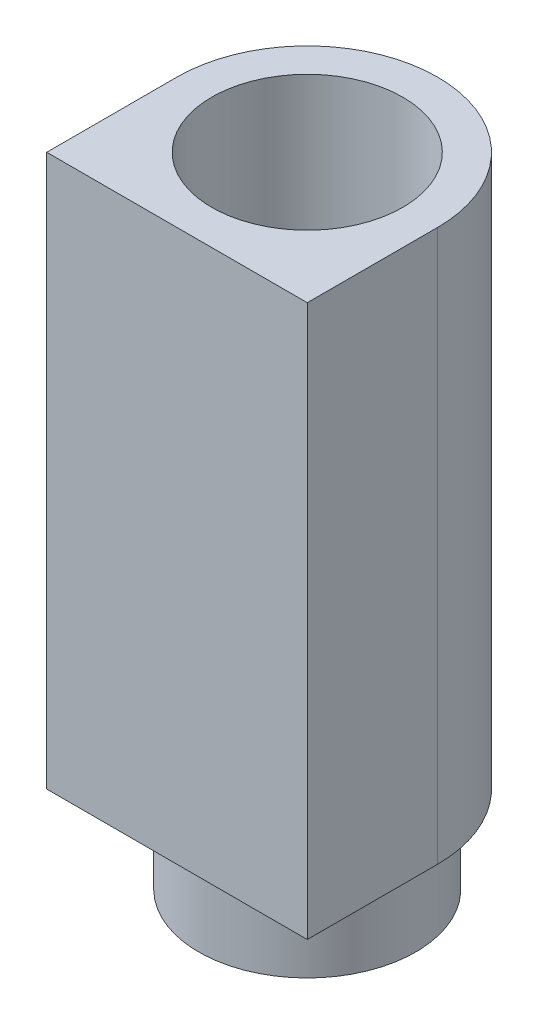
SolidWorks part; units mm, degrees
ref_plane "Front Plane" through (0, 0, 0) normal (0, 0, 1) x (1, 0, 0)
ref_plane "Top Plane" through (0, 0, 0) normal (0, 1, 0) x (1, 0, 0)
ref_plane "Right Plane" through (0, 0, 0) normal (1, 0, 0) x (0, 0, -1)
sketch "Sketch1" plane through (0, 0, 0) normal (0, 1, 0) x (1, 0, 0)
  line L2 (-30, 0) -> (-30, -30)
  line L3 (-30, -30) -> (30, -30)
  line L4 (30, 0) -> (30, -30)
  line L5 (-30, 30) -> (30, -30) construction
  line L6 (-30, -30) -> (30, 30) construction
  arc A0 (30, 0) -> (-30, 0) centre (0, 0) ccw
  point P0 (0, 0)
  dimension "D3" = 30
  dimension "D1" = 60
  dimension "D2" = 60
extrude "Boss-Extrude1" add sketch "Sketch1" along normal blind 127
sketch "Sketch3" plane through (0, 0, 0) normal (0, -1, 0) x (-1, 0, 0)
  circle A0 centre (0, 0) radius 25
  circle A1 centre (0, 0) radius 22
extrude "Boss-Extrude2" add sketch "Sketch3" along normal blind 20 contours A0
sketch "Sketch4" plane through (0, -20, 0) normal (0, -1, 0) x (-1, 0, 0)
  circle A0 centre (0, 0) radius 22
extrude "Cut-Extrude2" cut sketch "Sketch4" against normal through all
